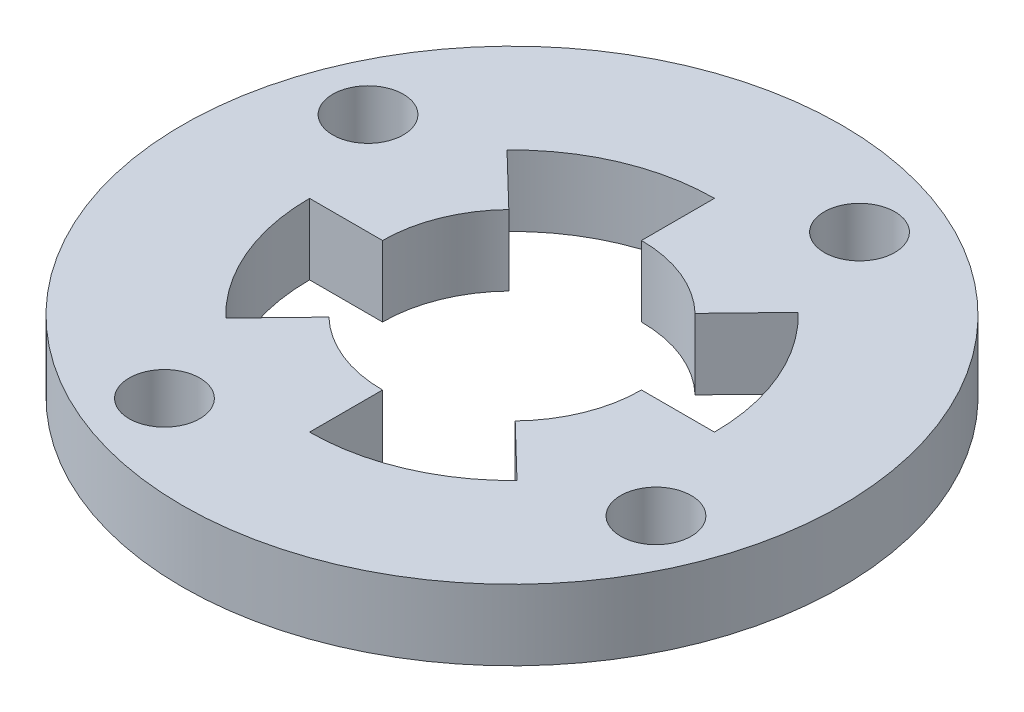
SolidWorks part; units mm, degrees
ref_plane "Front Plane" through (0, 0, 0) normal (0, 0, 1) x (1, 0, 0)
ref_plane "Top Plane" through (0, 0, 0) normal (0, 1, 0) x (1, 0, 0)
ref_plane "Right Plane" through (0, 0, 0) normal (1, 0, 0) x (0, 0, -1)
sketch "Sketch1" plane through (0, 0, 0) normal (0, 1, 0) x (1, 0, 0)
  line L0 (-5.5, 0) -> (-8.6, 0)
  line L2 (-6.1863, 5.9741) -> (-3.9564, 3.8206)
  line L3 (0, 5.5) -> (0, 8.6)
  line L4 (5.5, 0) -> (8.6, 0)
  line L5 (5.9741, 6.1863) -> (3.8206, 3.9564)
  line L6 (0, 5.5) -> (0, 8.6)
  line L7 (0, -5.5) -> (0, -8.6)
  line L8 (6.1863, -5.9741) -> (3.9564, -3.8206)
  line L9 (5.5, 0) -> (8.6, 0)
  line L10 (-5.5, 0) -> (-8.6, 0)
  line L11 (-5.9741, -6.1863) -> (-3.8206, -3.9564)
  line L12 (0, -5.5) -> (0, -8.6)
  line L13 (0, 0) -> (0, 5.5) construction
  line L14 (0, 0) -> (-5.0813, 2.1048) construction
  line L15 (-7.9454, 3.2911) -> (-12.9343, 5.3576) construction
  line L16 (0, 0) -> (-10.4398, 4.3243) construction
  arc A0 (-3.9564, 3.8206) -> (-5.5, 0) centre (0, 0) ccw
  arc A1 (0, 8.6) -> (-6.1863, 5.9741) centre (0, 0) ccw
  circle A2 centre (0, 0) radius 14
  arc A3 (8.6, 0) -> (5.9741, 6.1863) centre (0, 0) ccw
  arc A4 (3.8206, 3.9564) -> (0, 5.5) centre (0, 0) ccw
  arc A5 (0, -8.6) -> (6.1863, -5.9741) centre (0, 0) ccw
  arc A6 (3.9564, -3.8206) -> (5.5, 0) centre (0, 0) ccw
  arc A7 (-8.6, 0) -> (-5.9741, -6.1863) centre (0, 0) ccw
  arc A8 (-3.8206, -3.9564) -> (0, -5.5) centre (0, 0) ccw
  circle A9 centre (-10.4398, 4.3243) radius 1.5
  arc A10 (-6.1863, 5.9741) -> (-8.6, 0) centre (0, 0) ccw construction
  circle A11 centre (4.3243, 10.4398) radius 1.5
  circle A12 centre (10.4398, -4.3243) radius 1.5
  circle A13 centre (-4.3243, -10.4398) radius 1.5
  dimension "D1" = 11
  dimension "D2" = 17.2
  dimension "D5" = 28
  dimension "D7" = 3
  dimension "D3" = 44
  dimension "D6" = 22.5
  dimension "D9" = 11.3
  dimension "D4" = 4
  dimension "D8" = 4
extrude "Boss-Extrude1" add sketch "Sketch1" along normal blind 3 contours A2 A13 A12 A11 A9 A8 L11 A7 L0 A0 L2 A1 L3 A4 L5 A3 L4 A6 L8 A5 L7
